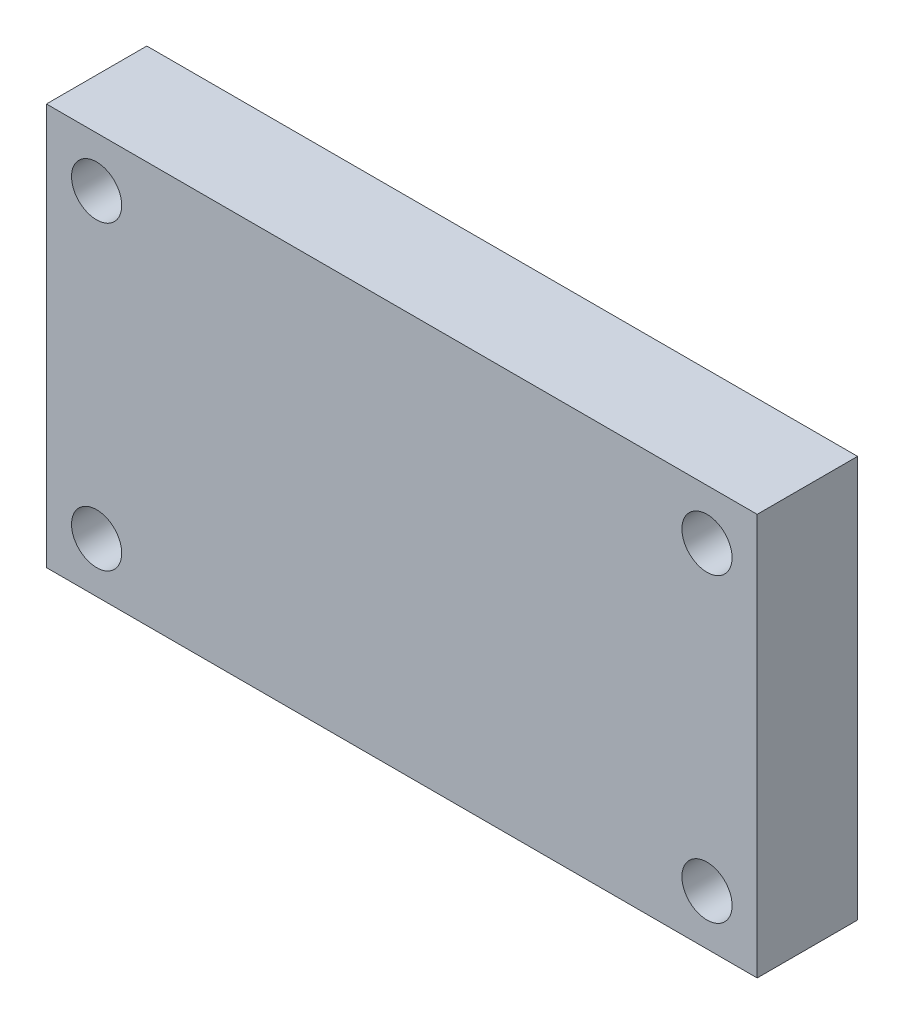
SolidWorks part; units mm, degrees
ref_plane "Front Plane" through (0, 0, 0) normal (0, 0, 1) x (1, 0, 0)
ref_plane "Top Plane" through (0, 0, 0) normal (0, 1, 0) x (1, 0, 0)
ref_plane "Right Plane" through (0, 0, 0) normal (1, 0, 0) x (0, 0, -1)
sketch "Sketch1" plane through (0, 0, 0) normal (0, 0, 1) x (1, 0, 0)
  line L0 (5, 0) -> (5, -5)
  line L1 (0, 0) -> (35.4, 0)
  line L2 (0, 0) -> (0, -20)
  line L3 (0, -20) -> (35.4, -20)
  line L4 (35.4, 0) -> (35.4, -20)
  line L5 (0, -15) -> (5, -15)
  line L6 (0, -5) -> (5, -5)
  line L7 (5, -5) -> (5, 0)
  line L8 (30.4, 0) -> (30.4, -5)
  line L9 (30.4, -5) -> (35.4, -5)
  line L10 (5, -15) -> (5, -20)
  line L11 (35.4, -15) -> (30.4, -15)
  line L12 (30.4, -15) -> (30.4, -20)
  circle A0 centre (2.5, -2.5) radius 1.25
  circle A1 centre (32.9, -2.5) radius 1.25
  circle A2 centre (32.9, -17.5) radius 1.25
  circle A3 centre (2.5, -17.5) radius 1.25
  point P24 (0, 0)
  point P26 (2.5, -5)
  point P27 (0, 0)
  point P28 (0, 0)
  point P29 (5, -2.5)
  point P30 (0, 0)
  point P31 (5, -17.5)
  point P32 (33.3843, -17.5)
  point P33 (32.9, -5)
  dimension "D4" = 2.5
  dimension "D1" = 35.4
  dimension "D2" = 20
  dimension "D3" = 5
extrude "Boss-Extrude1" add sketch "Sketch1" along normal blind 5 contours L12 L11 L4 L9 L8 L1 L0 L6 L2 L5 L10 L3 | L2 L6 L0 L1 A0 | L8 L9 L4 L1 A1 | L11 L12 L3 L4 A2 | L10 L5 L2 L3 A3
